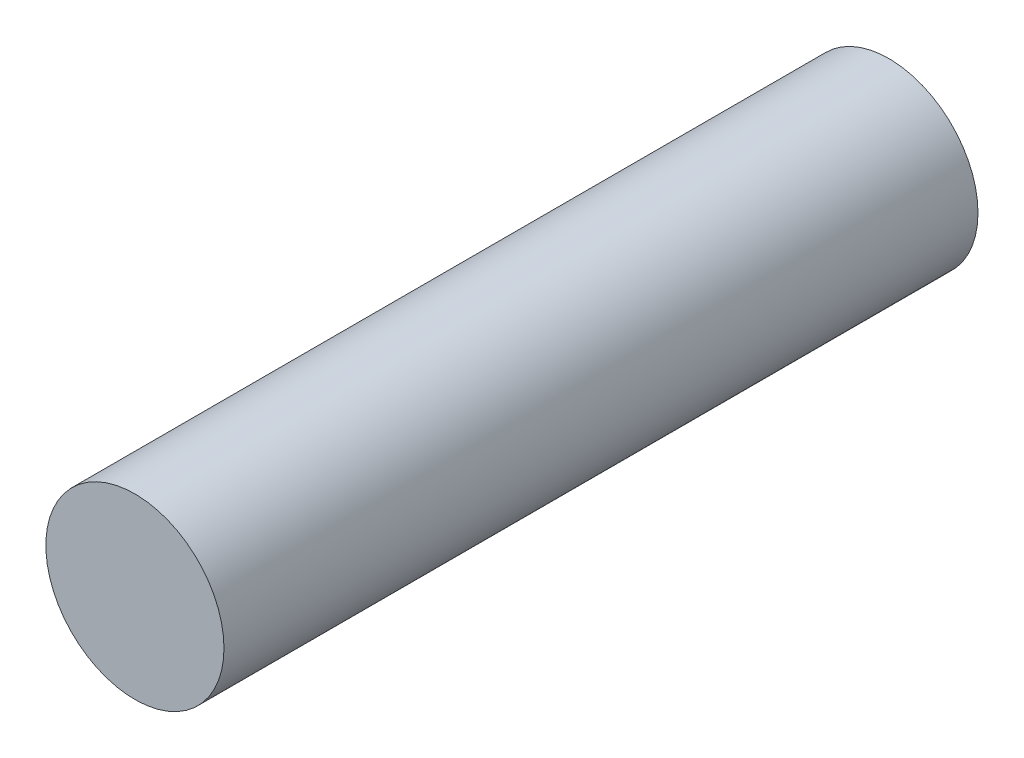
SolidWorks part; units mm, degrees
ref_plane "Front Plane" through (0, 0, 0) normal (0, 0, 1) x (1, 0, 0)
ref_plane "Top Plane" through (0, 0, 0) normal (0, 1, 0) x (1, 0, 0)
ref_plane "Right Plane" through (0, 0, 0) normal (1, 0, 0) x (0, 0, -1)
sketch "Sketch1" plane through (0, 0, 0) normal (0, 0, 1) x (1, 0, 0)
  circle A0 centre (0, 0) radius 5.1308
  dimension "D1" = 10.2616
extrude "Boss-Extrude1" add sketch "Sketch1" along normal blind 43.434
